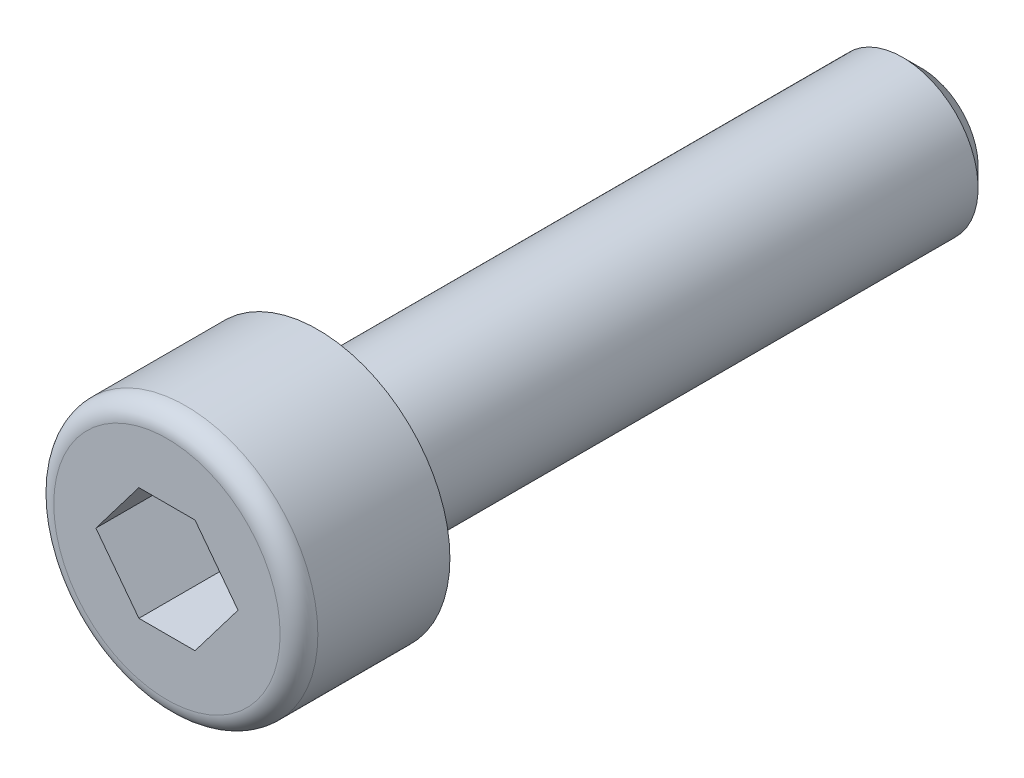
SolidWorks part; units mm, degrees
ref_plane "Plane1" through (0, 0, 0) normal (0, 0, 1) x (1, 0, 0)
ref_plane "Plane2" through (0, 0, 0) normal (0, 1, 0) x (1, 0, 0)
ref_plane "Plane3" through (0, 0, 0) normal (1, 0, 0) x (0, 0, -1)
sketch "Esquisse1" plane through (0, 0, 0) normal (0, 0, 1) x (1, 0, 0)
  circle A0 centre (0, 0) radius 3.5
  dimension "D1" = 7
extrude "Base-Extrusion" add sketch "Esquisse1" along normal blind 4
sketch "Esquisse2" plane through (0, 0, 0) normal (0, 0, -1) x (-1, 0, 0)
  circle A0 centre (0, 0) radius 2
  circle A1 centre (0, 0) radius 3.5 construction
  dimension "D1" = 4
extrude "Boss.-Extru.1" add sketch "Esquisse2" along normal blind 16
sketch "Esquisse3" plane through (0, 0, 4) normal (0, 0, 1) x (1, 0, 0)
  line L0 (0, 0) -> (0, 4.2257) construction
  line L1 (0, 0) -> (4.4294, 0) construction
  line L2 (1.884, 0) -> (0.744, 1.5)
  line L3 (0.744, 1.5) -> (-0.744, 1.5)
  line L4 (-0.744, 1.5) -> (-1.884, 0)
  line L5 (-1.884, 0) -> (-0.744, -1.5)
  line L6 (-0.744, -1.5) -> (0.744, -1.5)
  line L7 (0.744, -1.5) -> (1.884, 0)
  dimension "D1" = 3
  dimension "D2" = 3
extrude "Enlèv. mat.-Extru.1" cut sketch "Esquisse3" against normal blind 4
fillet "Congé1" radius 0.5
chamfer "Chanfrein1" distance 0.5 angle 45
